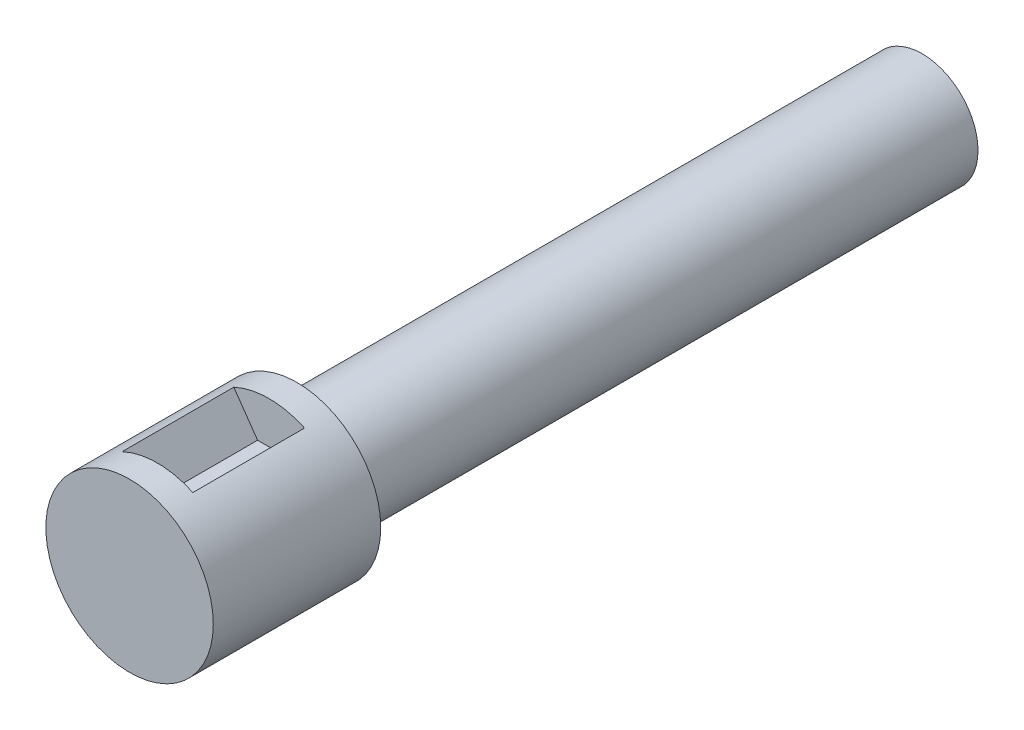
SolidWorks part; units mm, degrees
ref_plane "Front Plane" through (0, 0, 0) normal (0, 0, 1) x (1, 0, 0)
ref_plane "Top Plane" through (0, 0, 0) normal (0, 1, 0) x (1, 0, 0)
ref_plane "Right Plane" through (0, 0, 0) normal (1, 0, 0) x (0, 0, -1)
sketch "Sketch1" plane through (0, 0, 0) normal (0, 0, 1) x (1, 0, 0)
  circle A0 centre (0, 0) radius 9.525
extrude "Boss-Extrude1" add sketch "Sketch1" along normal blind 19.05
sketch "Sketch2" plane through (0, 0, 0) normal (0, 0, -1) x (-1, 0, 0)
  circle A0 centre (0, 0) radius 6.35
extrude "Boss-Extrude2" add sketch "Sketch2" along normal blind 71.12
sketch "Sketch3" plane through (0, 0, -71.12) normal (0, 0, -1) x (-1, 0, 0)
  line L1 (-1.2778, 1.524) -> (1.2778, 1.524)
  line L2 (0, 1.524) -> (-1.2778, 1.524)
  line L5 (-1.2778, -1.524) -> (1.2778, -1.524)
  line L6 (0, -1.524) -> (-1.2778, -1.524)
  arc A0 (1.2778, -1.524) -> (1.2778, 1.524) centre (0, 0) ccw
  arc A2 (-1.2778, 1.524) -> (-1.2778, -1.524) centre (0, 0) ccw
  dimension "D1" = 3.9776
extrude "Cut-Extrude1" cut sketch "Sketch3" against normal blind 9.144
sketch "Sketch4" plane through (0, 0, 19.05) normal (0, 0, 1) x (1, 0, 0)
  line L1 (0, 4.7625) -> (-1.3081, 4.7625)
  line L2 (-1.3081, 4.7625) -> (-4.0198, 8.6352)
  line L3 (0, 4.7625) -> (1.3194, 4.7625)
  line L4 (1.3194, 4.7625) -> (4.0283, 8.6312)
  circle A0 centre (0, 0) radius 9.525 construction
  arc A1 (4.0283, 8.6312) -> (-4.0198, 8.6352) centre (0, 0) ccw
  dimension "D1" = 125
  dimension "D2" = 125
extrude "Cut-Extrude2" cut sketch "Sketch4" against normal blind 12.7 from offset 3.175
